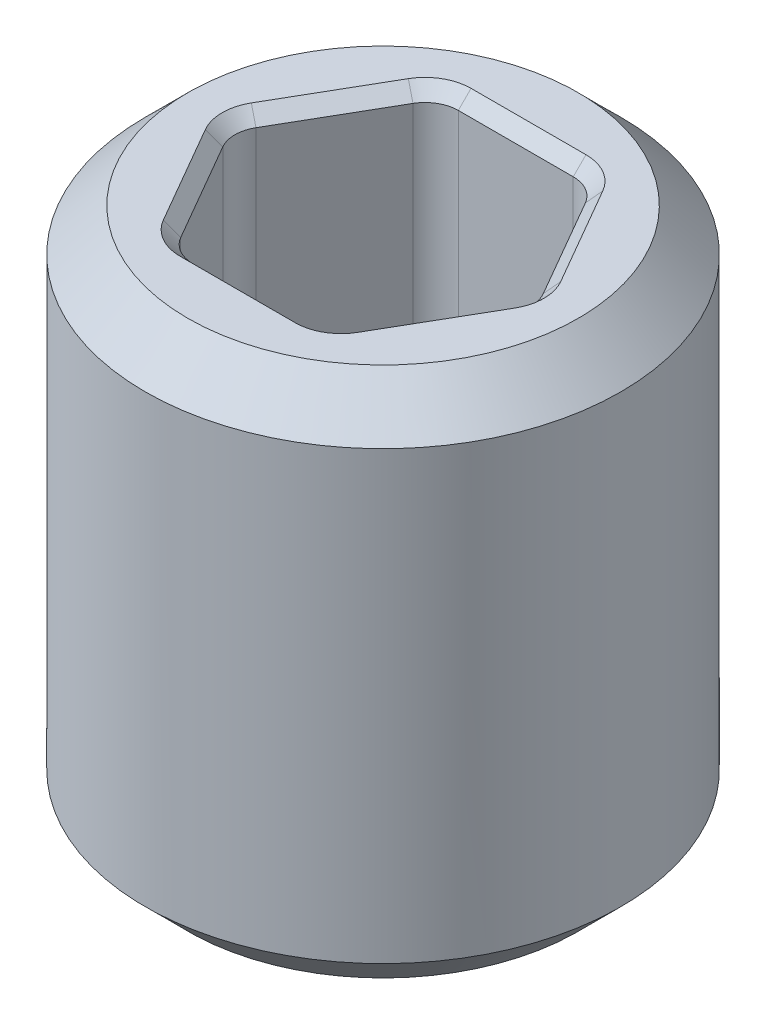
SolidWorks part; units mm, degrees
ref_plane "Front Plane" through (0, 0, 0) normal (0, 0, 1) x (1, 0, 0)
ref_plane "Top Plane" through (0, 0, 0) normal (0, 1, 0) x (1, 0, 0)
ref_plane "Right Plane" through (0, 0, 0) normal (1, 0, 0) x (0, 0, -1)
sketch "Sketch1" plane through (0, 0, 0) normal (0, 0, 1) x (1, 0, 0)
  line L0 (0, -1.7042) -> (0, -1.1626) construction
  line L1 (1.4224, -1.5875) -> (1.4224, 1.5875)
  line L2 (1.4224, 1.5875) -> (0, 1.5875)
  line L3 (0, 1.5875) -> (0, -1.5875)
  line L4 (0, -1.5875) -> (1.4224, -1.5875)
  dimension "D1" = 3.175
  dimension "D2" = 2.8448
revolve "Revolve1" add sketch "Sketch1" angle 360 about L0
sketch "Sketch3" plane through (0, 0, 0) normal (0, 1, 0) x (1, 0, 0)
  line L1 (0.9165, 0) -> (0.4583, 0.7938)
  line L2 (0.4583, 0.7938) -> (-0.4583, 0.7937)
  line L3 (-0.4583, 0.7937) -> (-0.9165, 0)
  line L4 (-0.9165, 0) -> (-0.4583, -0.7938)
  line L5 (-0.4583, -0.7938) -> (0.4583, -0.7937)
  line L6 (0.4583, -0.7937) -> (0.9165, 0)
  circle A0 centre (0, 0) radius 0.7937 construction
  dimension "D1" = 1.5875
extrude "Cut-Extrude1" cut sketch "Sketch3" against normal through all both and the other way through all contours L2 L3 L4 L5 L6 L1
fillet "Fillet1" radius 0.1984 6 edges at (0.4583, 0, -0.7938) (0.9165, 0, 0) (0.4583, 0, 0.7937) (-0.4583, 0, 0.7938) (-0.9165, 0, 0) (-0.4583, 0, -0.7937)
chamfer "Chamfer1" distance 0.254 angle 45 2 edges at (0, -1.5875, -1.4224) (0, 1.5875, -1.4224)
chamfer "Chamfer2" distance 0.0762 angle 45 24 edges at (0.6874, 1.5875, -0.3969) (0.4429, 1.5875, -0.7672) (0.8858, 1.5875, 0) (0, 1.5875, -0.7937) (0.6874, 1.5875, 0.3969) (-0.4429, 1.5875, -0.7672) (0.4429, 1.5875, 0.7672) (-0.6874, 1.5875, -0.3969) (0, 1.5875, 0.7937) (-0.8858, 1.5875, 0) (-0.4429, 1.5875, 0.7672) (-0.6874, 1.5875, 0.3969) (0.6874, -1.5875, 0.3969) (0.8858, -1.5875, 0) (0.4429, -1.5875, 0.7672) (0.6874, -1.5875, -0.3969) (0, -1.5875, 0.7937) (0.4429, -1.5875, -0.7672) (-0.4429, -1.5875, 0.7672) (0, -1.5875, -0.7937) (-0.6874, -1.5875, 0.3969) (-0.4429, -1.5875, -0.7672) (-0.8858, -1.5875, 0) (-0.6874, -1.5875, -0.3969)
